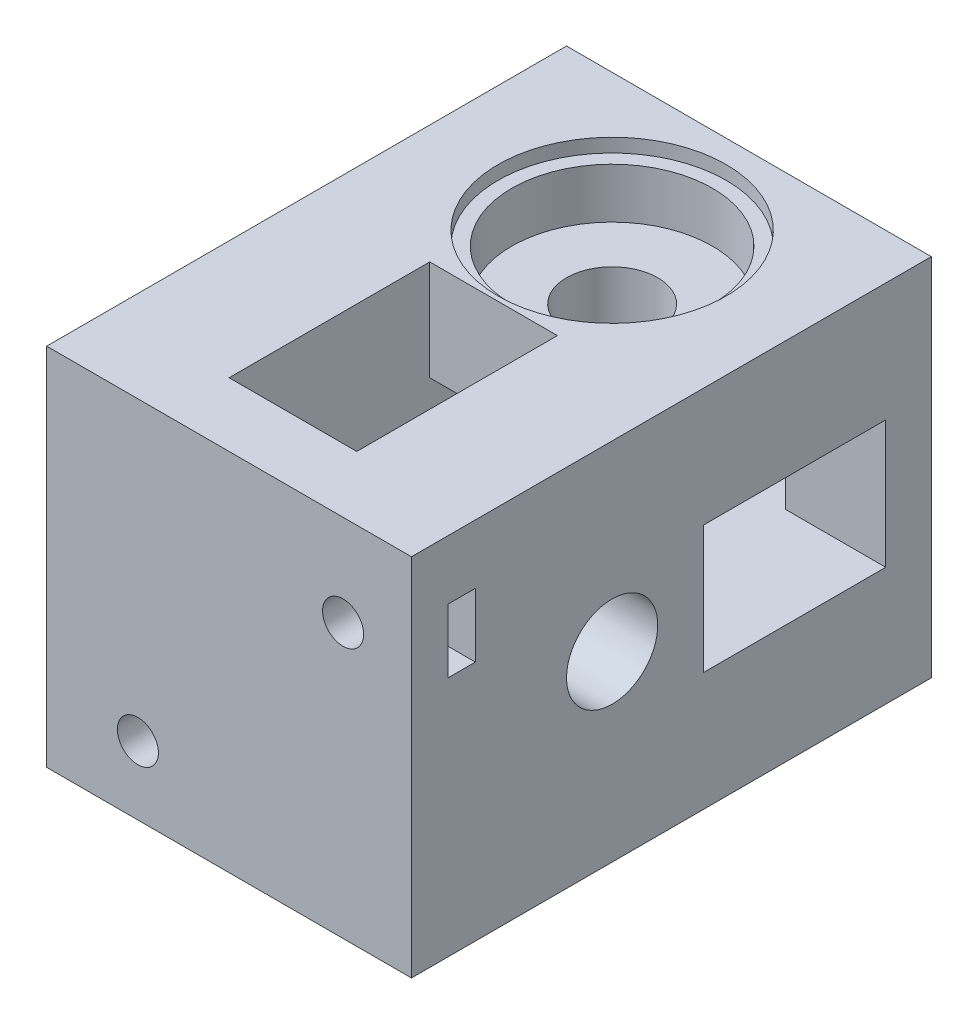
SolidWorks part; units mm, degrees
ref_plane "Plan de face" through (0, 0, 0) normal (0, 0, 1) x (1, 0, 0)
ref_plane "Plan de dessus" through (0, 0, 0) normal (0, 1, 0) x (1, 0, 0)
ref_plane "Plan de droite" through (0, 0, 0) normal (1, 0, 0) x (0, 0, -1)
sketch "Esquisse1" plane through (0, 0, 0) normal (0, 0, 1) x (1, 0, 0)
  line L1 (-40, 40) -> (0, 40)
  line L2 (-40, 40) -> (-40, 0)
  line L3 (-40, 0) -> (0, 0)
  line L4 (0, 40) -> (0, 0)
  dimension "D1" = 40
  dimension "D2" = 40
extrude "Boss.-Extru.1" add sketch "Esquisse1" along normal blind 50
sketch "Esquisse2" plane through (0, 40, 0) normal (0, 1, 0) x (1, 0, 0)
  line L0 (0, 0) -> (-40, 0) construction
  line L1 (-40, -50) -> (-40, 0) construction
  circle A0 centre (-20, -15) radius 5
  dimension "D1" = 10
  dimension "D2" = 15
  dimension "D3" = 20
extrude "Enlèv. mat.-Extru.1" cut sketch "Esquisse2" against normal through all
sketch "Esquisse3" plane through (-40, 0, 0) normal (-1, 0, 0) x (0, 0, 1)
  line L0 (50, 40) -> (50, 0) construction
  line L1 (50, 40) -> (0, 40) construction
  circle A0 centre (35, 20) radius 5
  dimension "D1" = 10
  dimension "D2" = 15
  dimension "D3" = 20
extrude "Enlèv. mat.-Extru.2" cut sketch "Esquisse3" against normal through all
sketch "Esquisse4" plane through (-40, 0, 0) normal (-1, 0, 0) x (0, 0, 1)
  line L1 (22, 27) -> (0, 27)
  line L2 (22, 27) -> (22, 13)
  line L3 (22, 13) -> (0, 13)
  line L4 (0, 27) -> (0, 13)
  line L5 (0, 40) -> (0, 0) construction
  line L6 (50, 0) -> (0, 0) construction
  line L7 (50, 40) -> (0, 40) construction
  dimension "D1" = 14
  dimension "D2" = 22
  dimension "D3" = 0
  dimension "D4" = 13
  dimension "D5" = 13
extrude "Enlèv. mat.-Extru.3" cut sketch "Esquisse4" against normal blind 29
sketch "Esquisse5" plane through (0, 0, 0) normal (0, -1, 0) x (1, 0, 0)
  line L0 (-40, 50) -> (0, 50) construction
  line L1 (-13, 25) -> (-27, 25)
  line L2 (-13, 25) -> (-13, 45)
  line L3 (-13, 45) -> (-27, 45)
  line L4 (-27, 25) -> (-27, 45)
  line L5 (-40, 50) -> (-40, 0) construction
  dimension "D1" = 20
  dimension "D2" = 5
  dimension "D3" = 14
  dimension "D4" = 13
extrude "Enlèv. mat.-Extru.4" cut sketch "Esquisse5" against normal blind 29
sketch "Esquisse6" plane through (0, 0, 0) normal (1, 0, 0) x (0, 0, -1)
  line L1 (-5, 27) -> (-25, 27)
  line L2 (0, 0) -> (0, 40) construction
  line L3 (-5, 13) -> (-25, 13)
  line L4 (-25, 27) -> (-25, 13)
  line L5 (-50, 0) -> (0, 0) construction
  line L6 (-5, 27) -> (-5, 13)
  dimension "D1" = 14
  dimension "D2" = 5
  dimension "D3" = 13
  dimension "D4" = 20
extrude "Enlèv. mat.-Extru.5" cut sketch "Esquisse6" against normal blind 24
sketch "Esquisse7" plane through (0, 40, 0) normal (0, 1, 0) x (1, 0, 0)
  line L0 (0, -50) -> (-40, -50) construction
  line L1 (-27, -50) -> (-13, -50)
  line L2 (-27, -50) -> (-27, -28)
  line L3 (-27, -28) -> (-13, -28)
  line L4 (-13, -50) -> (-13, -28)
  line L5 (-40, -50) -> (-40, 0) construction
  dimension "D1" = 14
  dimension "D2" = 22
  dimension "D3" = 13
extrude "Enlèv. mat.-Extru.6" cut sketch "Esquisse7" against normal blind 24
sketch "Esquisse10" plane through (0, 40, 0) normal (0, 1, 0) x (1, 0, 0)
  circle A0 centre (-20, -15) radius 11
  dimension "D1" = 22
extrude "Enlèv. mat.-Extru.9" cut sketch "Esquisse10" against normal blind 7
sketch "Esquisse11" plane through (0, 40, 0) normal (0, 1, 0) x (1, 0, 0)
  circle A0 centre (-20, -15) radius 12.5
  dimension "D1" = 25
extrude "Enlèv. mat.-Extru.10" cut sketch "Esquisse11" against normal blind 1.5
sketch "Esquisse14" plane through (-40, 0, 0) normal (-1, 0, 0) x (0, 0, 1)
  circle A0 centre (35, 20) radius 11
  dimension "D1" = 22
extrude "Enlèv. mat.-Extru.11" cut sketch "Esquisse14" against normal blind 7
sketch "Esquisse15" plane through (-40, 0, 0) normal (-1, 0, 0) x (0, 0, 1)
  circle A0 centre (35, 20) radius 12.5
  dimension "D1" = 25
extrude "Enlèv. mat.-Extru.12" cut sketch "Esquisse15" against normal blind 1.5
sketch "Esquisse16" plane through (0, 0, 50) normal (0, 0, 1) x (1, 0, 0)
  line L1 (0, 0) -> (-40, 0)
  line L2 (0, 0) -> (0, 40)
  line L3 (0, 40) -> (-40, 40)
  line L4 (-40, 0) -> (-40, 40)
  point P4 (-29.2801, 37.6842)
extrude "Boss.-Extru.2" add sketch "Esquisse16" along normal blind 7
sketch "Esquisse17" plane through (0, 0, 57) normal (0, 0, 1) x (1, 0, 0)
  line L0 (-40, 40) -> (-40, 0) construction
  line L1 (0, 40) -> (-40, 40) construction
  circle A0 centre (-30, 7.5) radius 2.25
  circle A1 centre (-7.5, 30) radius 2.25
  dimension "D1" = 4.5
  dimension "D2" = 4.5
  dimension "D3" = 10
  dimension "D4" = 10
  dimension "D5" = 32.5
  dimension "D6" = 32.5
extrude "Enlèv. mat.-Extru.13" cut sketch "Esquisse17" against normal blind 15
sketch "Esquisse18" plane through (0, 0, 0) normal (0, -1, 0) x (1, 0, 0)
  line L0 (-40, 57) -> (0, 57) construction
  line L1 (-26.5, 50) -> (-33.5, 50)
  line L2 (-26.5, 50) -> (-26.5, 53)
  line L3 (-26.5, 53) -> (-33.5, 53)
  line L4 (-33.5, 50) -> (-33.5, 53)
  line L5 (-40, 57) -> (-40, 0) construction
  dimension "D1" = 7
  dimension "D2" = 3
  dimension "D3" = 4
  dimension "D4" = 6.5
extrude "Enlèv. mat.-Extru.14" cut sketch "Esquisse18" against normal blind 12
sketch "Esquisse19" plane through (0, 0, 0) normal (1, 0, 0) x (0, 0, -1)
  line L0 (-57, 0) -> (-57, 40) construction
  line L1 (-50, 33.5) -> (-53, 33.5)
  line L2 (-50, 33.5) -> (-50, 26.5)
  line L3 (-50, 26.5) -> (-53, 26.5)
  line L4 (-53, 33.5) -> (-53, 26.5)
  line L5 (-57, 40) -> (0, 40) construction
  dimension "D1" = 7
  dimension "D2" = 3
  dimension "D3" = 4
  dimension "D4" = 6.5
extrude "Enlèv. mat.-Extru.15" cut sketch "Esquisse19" against normal blind 12
